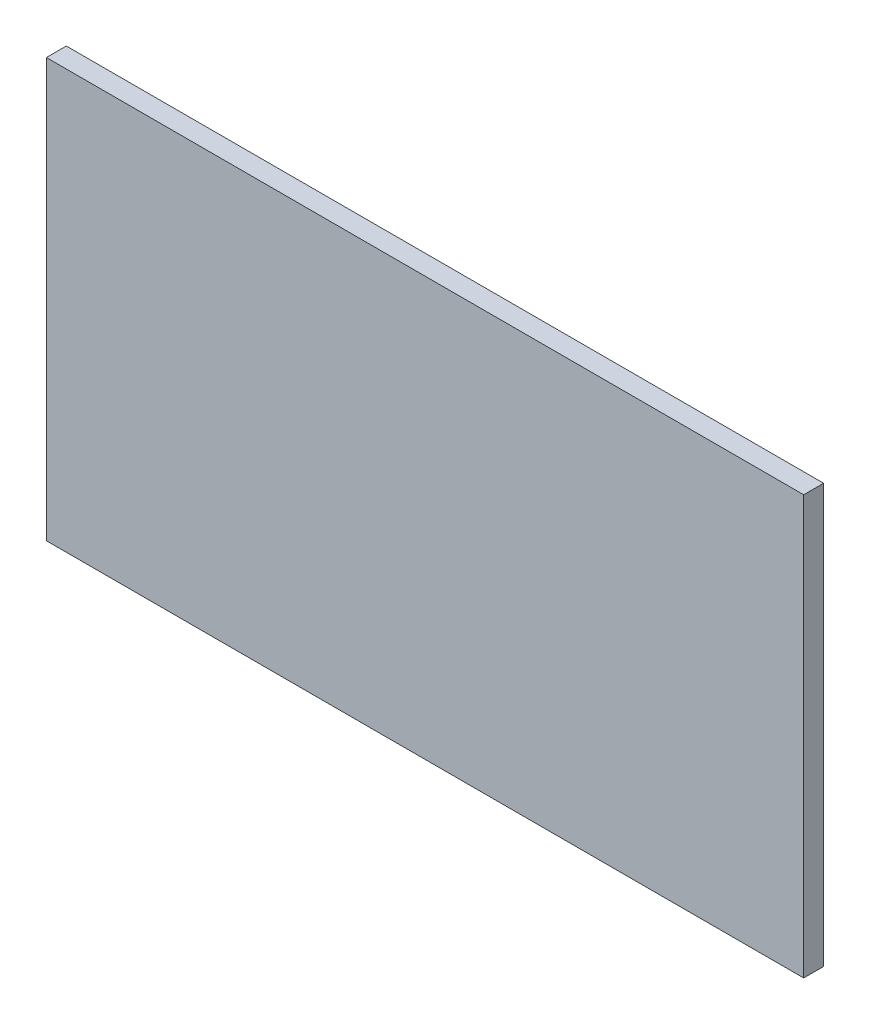
SolidWorks part; units mm, degrees
ref_plane "Plan de face" through (0, 0, 0) normal (0, 0, 1) x (1, 0, 0)
ref_plane "Plan de dessus" through (0, 0, 0) normal (0, 1, 0) x (1, 0, 0)
ref_plane "Plan de droite" through (0, 0, 0) normal (1, 0, 0) x (0, 0, -1)
sketch "Esquisse1" plane through (0, 0, 0) normal (0, 0, 1) x (1, 0, 0)
  line L1 (-190, 105) -> (190, 105)
  line L2 (-190, 105) -> (-190, -105)
  line L3 (-190, -105) -> (190, -105)
  line L4 (190, 105) -> (190, -105)
  dimension "D1" = 380
  dimension "D2" = 210
  dimension "D3" = 105
  dimension "D4" = 190
extrude "Boss.-Extru.1" add sketch "Esquisse1" along normal blind 10
